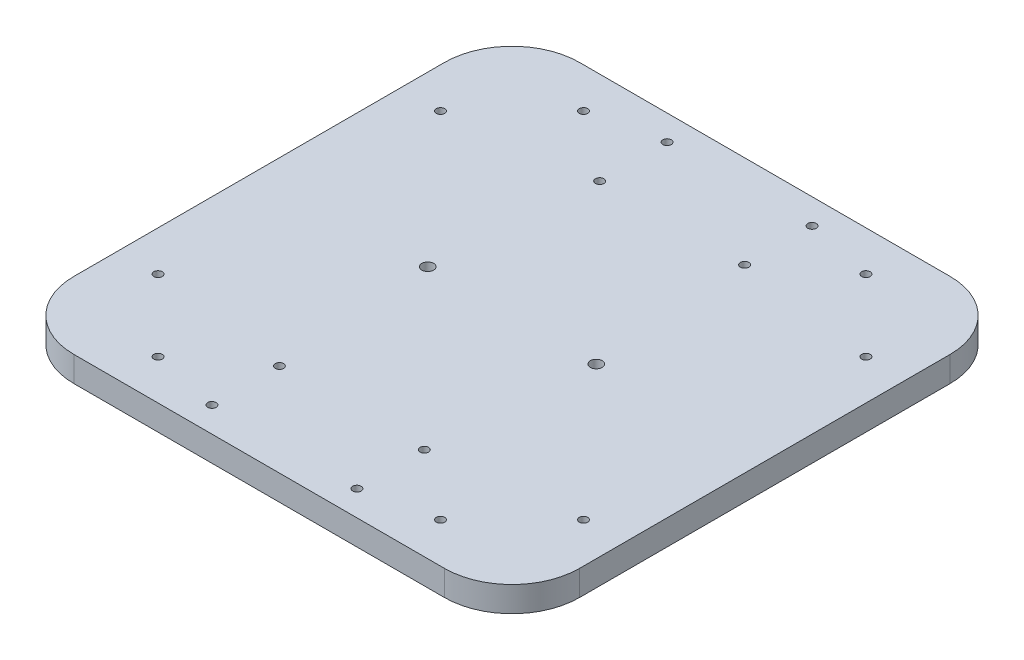
SolidWorks part; units mm, degrees
ref_plane "Front Plane" through (0, 0, 0) normal (0, 0, 1) x (1, 0, 0)
ref_plane "Top Plane" through (0, 0, 0) normal (0, 1, 0) x (1, 0, 0)
ref_plane "Right Plane" through (0, 0, 0) normal (1, 0, 0) x (0, 0, -1)
sketch "Sketch1" plane through (0, 0, 0) normal (0, 0, 1) x (1, 0, 0)
  line L8 (-150, -7.5) -> (150, -7.5)
  line L9 (-150, -7.5) -> (-150, 7.5)
  line L10 (-150, 7.5) -> (150, 7.5)
  line L11 (150, -7.5) -> (150, 7.5)
  line L12 (-150, -7.5) -> (150, 7.5) construction
  line L13 (-150, 7.5) -> (150, -7.5) construction
  point P0 (0, 0)
  dimension "D1" = 15
  dimension "D2" = 300
extrude "Boss-Extrude1" add sketch "Sketch1" along normal mid plane 300
sketch "Sketch5" plane through (0, -7.5, 0) normal (0, -1, 0) x (1, 0, 0)
  circle A0 centre (50, 0) radius 3.5
  circle A1 centre (-50, 0) radius 3.5
  dimension "D2" = 7
  dimension "D3" = 50
  dimension "D4" = 7
  dimension "D1" = 50
extrude "Cut-Extrude3" cut sketch "Sketch5" against normal through all both and the other way through all
ref_plane "Plane1" through (0, -57.5, 0) normal (0, -1, 0) x (-1, 0, 0)
sketch "Sketch7" plane through (0, -7.5, 0) normal (0, -1, 0) x (1, 0, 0)
  line L0 (-126.2132, 83.7868) -> (-83.7868, 126.2132) construction
  line L1 (-105, -105) -> (105, -105) construction
  line L2 (-105, -105) -> (-105, 105) construction
  line L3 (-105, 105) -> (105, 105) construction
  line L4 (105, -105) -> (105, 105) construction
  line L5 (-105, -105) -> (105, 105) construction
  line L6 (-105, 105) -> (105, -105) construction
  line L7 (-130.725, 85.9416) -> (-118.5355, 111.4645) construction
  line L8 (-124.0584, 79.275) -> (-98.5355, 91.4645) construction
  line L9 (-111.4645, 118.5355) -> (-85.9416, 130.725) construction
  line L10 (-91.4645, 98.5355) -> (-79.275, 124.0584) construction
  line L11 (85.9416, 130.725) -> (111.4645, 118.5355) construction
  line L12 (79.275, 124.0584) -> (91.4645, 98.5355) construction
  line L13 (83.7868, 126.2132) -> (126.2132, 83.7868) construction
  line L14 (98.5355, 91.4645) -> (124.0584, 79.275) construction
  line L15 (118.5355, 111.4645) -> (130.725, 85.9416) construction
  line L16 (130.725, -85.9416) -> (118.5355, -111.4645) construction
  line L17 (124.0584, -79.275) -> (98.5355, -91.4645) construction
  line L18 (126.2132, -83.7868) -> (83.7868, -126.2132) construction
  line L19 (91.4645, -98.5355) -> (79.275, -124.0584) construction
  line L20 (111.4645, -118.5355) -> (85.9416, -130.725) construction
  line L21 (-85.9416, -130.725) -> (-111.4645, -118.5355) construction
  line L22 (-79.275, -124.0584) -> (-91.4645, -98.5355) construction
  line L23 (-83.7868, -126.2132) -> (-126.2132, -83.7868) construction
  line L24 (-98.5355, -91.4645) -> (-124.0584, -79.275) construction
  line L25 (-118.5355, -111.4645) -> (-130.725, -85.9416) construction
  circle A0 centre (-105, 105) radius 5 construction
  circle A1 centre (-105, 105) radius 15 construction
  circle A2 centre (-83.7868, 126.2132) radius 5 construction
  circle A3 centre (-126.2132, 83.7868) radius 5 construction
  circle A4 centre (83.7868, 126.2132) radius 5 construction
  circle A5 centre (105, 105) radius 15 construction
  circle A6 centre (126.2132, 83.7868) radius 5 construction
  circle A7 centre (126.2132, -83.7868) radius 5 construction
  circle A8 centre (105, -105) radius 15 construction
  circle A9 centre (83.7868, -126.2132) radius 5 construction
  circle A10 centre (-83.7868, -126.2132) radius 5 construction
  circle A11 centre (-105, -105) radius 15 construction
  circle A12 centre (-126.2132, -83.7868) radius 5 construction
  point P0 (0, 0)
  point P11 (-105, 105)
  point P66 (0, 0)
  dimension "D2" = 10
  dimension "D3" = 30
  dimension "D5" = 10
  dimension "D1" = 210
  dimension "D4" = 45
  dimension "D6" = 60
  dimension "D7" = 4
sketch "Sketch8" plane through (0, -7.5, 0) normal (0, -1, 0) x (1, 0, 0)
  circle A0 centre (-126.2132, 83.7868) radius 2.5
  circle A1 centre (-83.7868, 126.2132) radius 2.5
  circle A2 centre (126.2132, 83.7868) radius 2.5
  circle A3 centre (83.7868, 126.2132) radius 2.5
  circle A4 centre (83.7868, -126.2132) radius 2.5
  circle A5 centre (126.2132, -83.7868) radius 2.5
  circle A6 centre (-126.2132, -83.7868) radius 2.5
  circle A7 centre (-83.7868, -126.2132) radius 2.5
  point P21 (0, 0)
  dimension "D1" = 5
  dimension "D2" = 4
extrude "Cut-Extrude5" cut sketch "Sketch8" against normal through all
fillet "Fillet4" radius 40 4 edges at (-150, 0, -150) (150, 0, -150) (150, 0, 150) (-150, 0, 150)
sketch "Sketch9" plane through (0, -7.5, 0) normal (0, -1, 0) x (-1, 0, 0)
  line L0 (0, 115) -> (0, -115) construction
  line L2 (43, -95) -> (-43, -95) construction
  line L3 (43, -95) -> (43, -135) construction
  line L4 (43, -135) -> (-43, -135) construction
  line L5 (-43, -95) -> (-43, -135) construction
  line L6 (43, -95) -> (-43, -135) construction
  line L7 (43, -135) -> (-43, -95) construction
  line L8 (43, 135) -> (-43, 135) construction
  line L9 (43, 135) -> (43, 95) construction
  line L10 (43, 95) -> (-43, 95) construction
  line L11 (-43, 135) -> (-43, 95) construction
  line L12 (43, 135) -> (-43, 95) construction
  line L13 (43, 95) -> (-43, 135) construction
  circle A0 centre (43, -135) radius 2.5
  circle A1 centre (-43, -135) radius 2.5
  circle A2 centre (-43, -95) radius 2.5
  circle A3 centre (43, -95) radius 2.5
  circle A4 centre (-43, 95) radius 2.5
  circle A5 centre (-43, 135) radius 2.5
  circle A6 centre (43, 135) radius 2.5
  circle A7 centre (43, 95) radius 2.5
  point P4 (0, 0)
  dimension "D4" = 5
  dimension "D1" = 230
  dimension "D2" = 40
  dimension "D3" = 86
extrude "Cut-Extrude6" cut sketch "Sketch9" against normal through all
